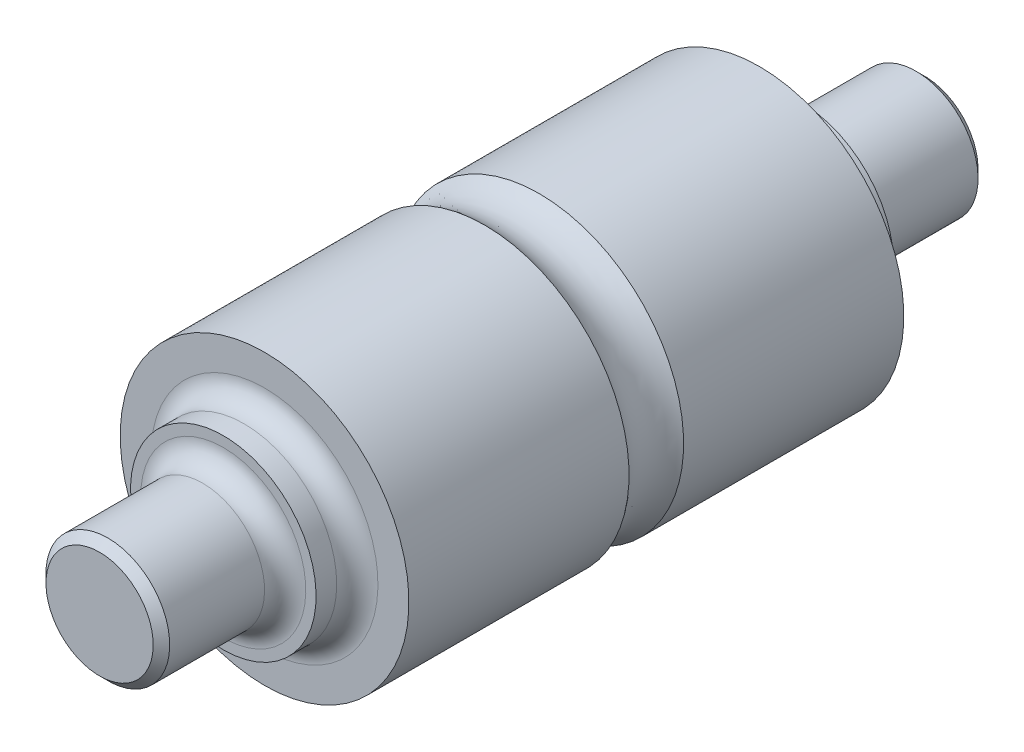
SolidWorks part; units mm, degrees
material "AISI 304"
ref_plane "Plano frontal" through (0, 0, 0) normal (0, 0, 1) x (1, 0, 0)
ref_plane "Plano superior" through (0, 0, 0) normal (0, 1, 0) x (1, 0, 0)
ref_plane "Plano direito" through (0, 0, 0) normal (1, 0, 0) x (0, 0, -1)
sketch "Esboço1" plane through (0, 0, 0) normal (1, 0, 0) x (0, 0, -1)
  line L0 (-100, 0) -> (100, 0) construction
  line L1 (100, 0) -> (100, 15)
  line L2 (100, 15) -> (70, 15)
  line L3 (70, 15) -> (70, 22.5)
  line L4 (-100, 0) -> (-100, 15)
  line L5 (-100, 15) -> (-70, 15)
  line L6 (-70, 15) -> (-70, 22.5)
  line L7 (-70, 22.5) -> (-60, 22.5)
  line L8 (-60, 22.5) -> (-60, 35)
  line L9 (-60, 35) -> (-6.6144, 35)
  line L10 (6.6144, 35) -> (60, 35)
  line L11 (60, 35) -> (60, 22.5)
  line L12 (60, 22.5) -> (70, 22.5)
  line L13 (-100, 0) -> (100, 0)
  arc A0 (-6.6144, 35) -> (6.6144, 35) centre (0, 42.5) ccw
  point P14 (0, 0)
  dimension "D7" = 65
  dimension "D8" = 10
  dimension "D1" = 200
  dimension "D2" = 30
  dimension "D3" = 45
  dimension "D4" = 70
  dimension "D5" = 30
  dimension "D6" = 10
revolve "Revolução1" add sketch "Esboço1" angle 360 about L0
chamfer "Chanfro1" distance 2 angle 45 2 edges at (0, -15, -100) (0, -15, 100)
fillet "Filete1" radius 5 4 edges at (0, -15, -70) (0, -22.5, -60) (0, -22.5, 60) (0, -15, 70)
